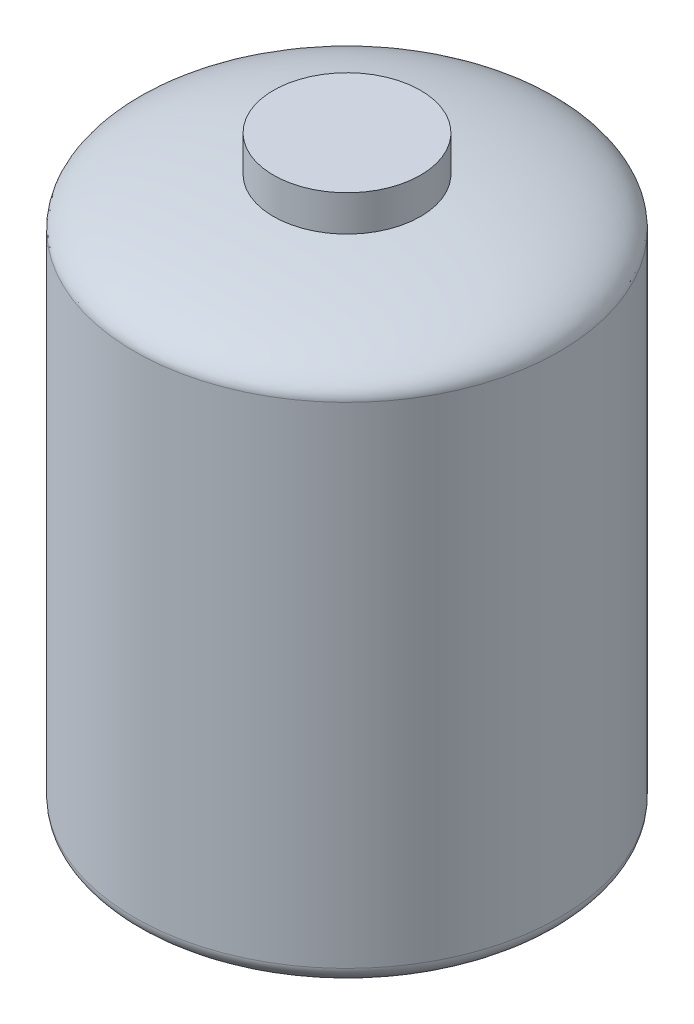
SolidWorks part; units mm, degrees
ref_plane "Front Plane" through (0, 0, 0) normal (0, 0, 1) x (1, 0, 0)
ref_plane "Top Plane" through (0, 0, 0) normal (0, 1, 0) x (1, 0, 0)
ref_plane "Right Plane" through (0, 0, 0) normal (1, 0, 0) x (0, 0, -1)
sketch "Sketch1" plane through (0, 0, 0) normal (0, 0, 1) x (1, 0, 0)
  line L0 (0, 1205.8359) -> (0, -1318.2973) construction
  line L1 (0, 913.7142) -> (-225, 913.7142)
  line L2 (-650, 658.7142) -> (-650, -841.2858)
  line L3 (-1032.8581, -91.2858) -> (733.2389, -91.2858) construction
  line L4 (-225, 913.7142) -> (-225, 804.1317)
  line L5 (0, -996.2858) -> (0, 913.7142)
  ellipse E0 centre (0, -841.2858) end of major axis (650, -841.2858) minor radius 155 (-650, -841.2858) -> (0, -996.2858) ccw
  ellipse E1 centre (0, 658.7142) end of major axis (650, 658.7142) minor radius 155 (-650, 658.7142) -> (-225, 804.1317) cw
  dimension "D1" = 1500
  dimension "D2" = 450
  dimension "D3" = 100
  dimension "D4" = 650
revolve "Revolve1" add sketch "Sketch1" angle 360 about L5
